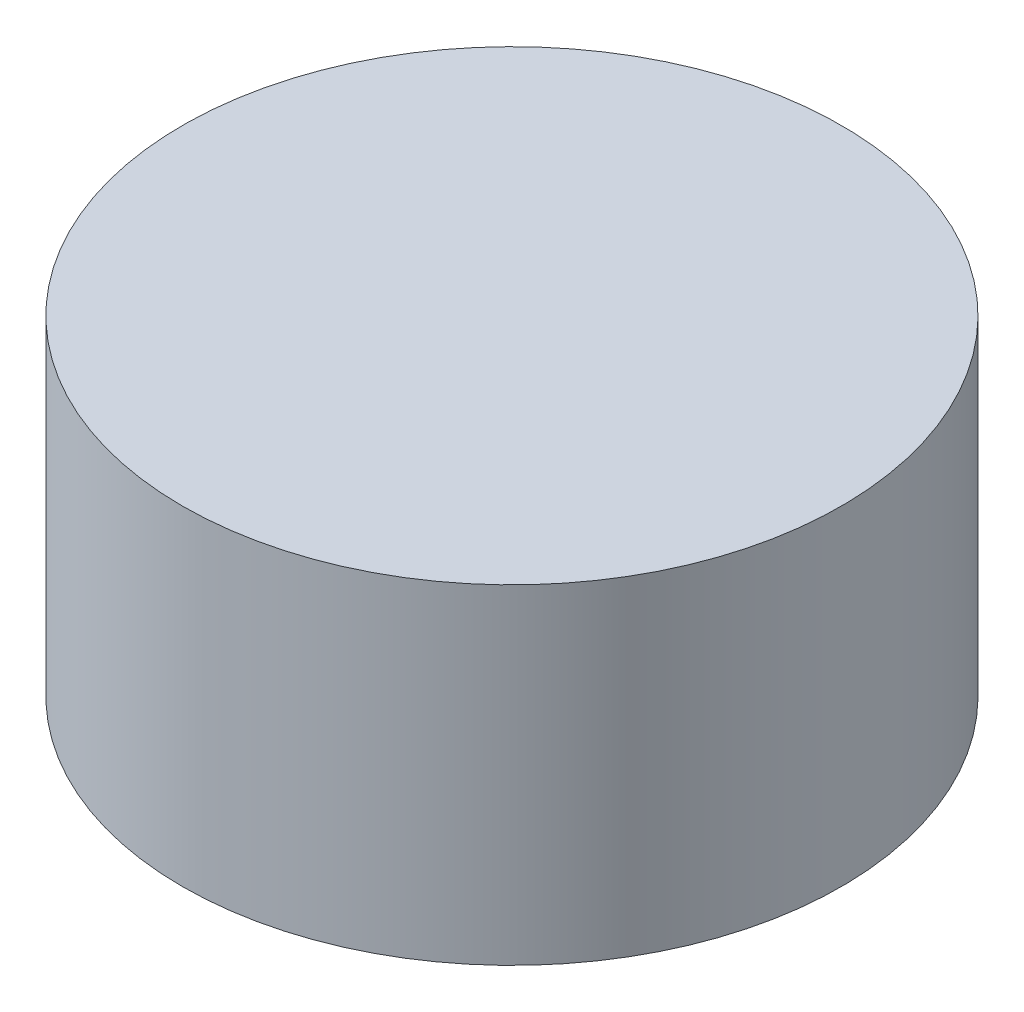
SolidWorks part; units mm, degrees
ref_plane "Front Plane" through (0, 0, 0) normal (0, 0, 1) x (1, 0, 0)
ref_plane "Top Plane" through (0, 0, 0) normal (0, 1, 0) x (1, 0, 0)
ref_plane "Right Plane" through (0, 0, 0) normal (1, 0, 0) x (0, 0, -1)
sketch "Sketch1" plane through (0, 0, 0) normal (0, 1, 0) x (1, 0, 0)
  circle A0 centre (0, 0) radius 10
  dimension "20" = 20
extrude "Boss-Extrude1" add sketch "Sketch1" along normal blind 10
